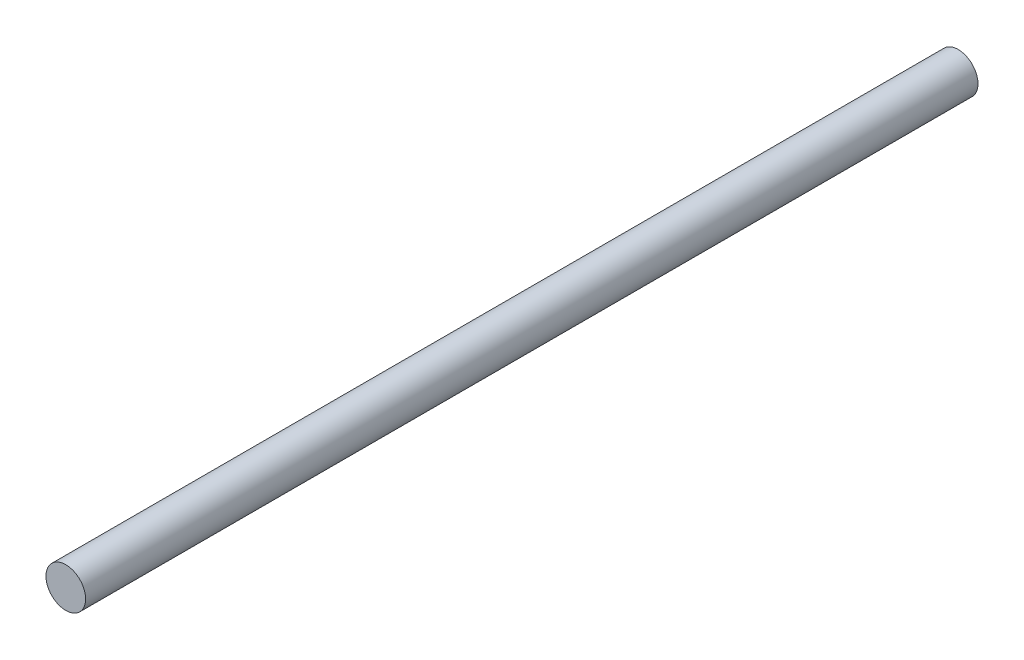
SolidWorks part; units mm, degrees
ref_plane "前视基准面" through (0, 0, 0) normal (0, 0, 1) x (1, 0, 0)
ref_plane "上视基准面" through (0, 0, 0) normal (0, 1, 0) x (1, 0, 0)
ref_plane "右视基准面" through (0, 0, 0) normal (1, 0, 0) x (0, 0, -1)
sketch "草图1" plane through (0, 0, 0) normal (0, 0, 1) x (1, 0, 0)
  circle A0 centre (0, 0) radius 4
extrude "凸台-拉伸1" add sketch "草图1" along normal blind 180
